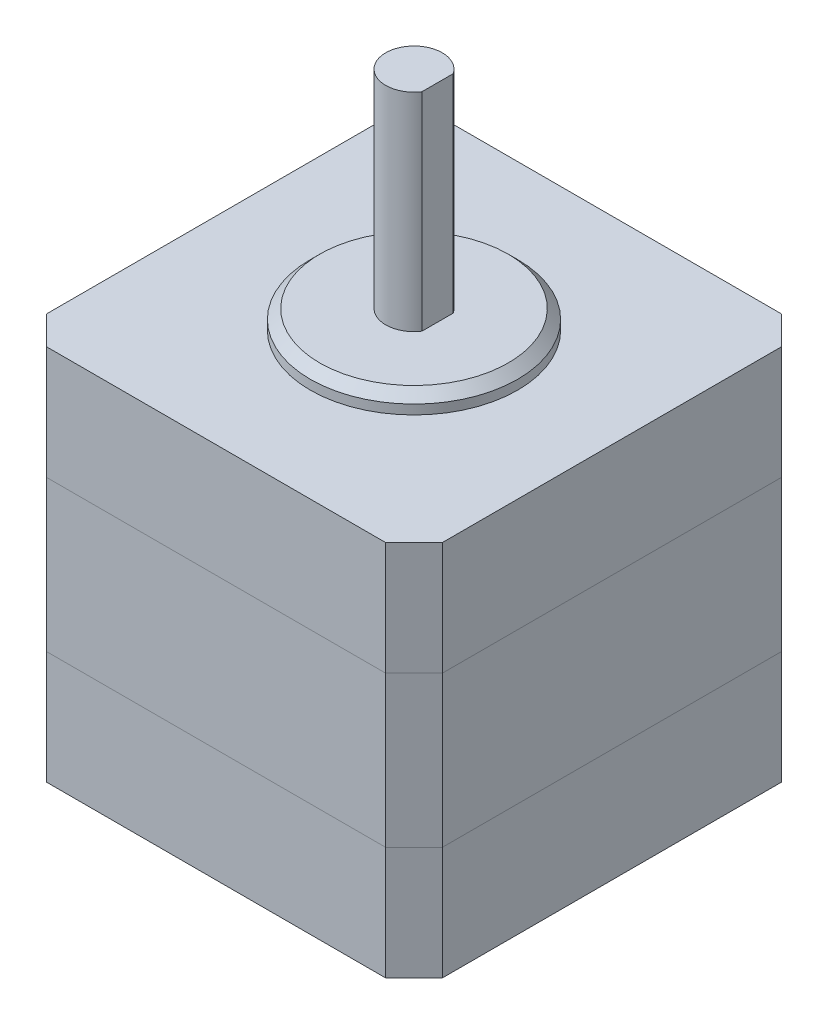
SolidWorks part; units mm, degrees
material "Cast Stainless Steel"
ref_plane "Front Plane" through (0, 0, 0) normal (0, 0, 1) x (1, 0, 0)
ref_plane "Top Plane" through (0, 0, 0) normal (0, 1, 0) x (1, 0, 0)
ref_plane "Right Plane" through (0, 0, 0) normal (1, 0, 0) x (0, 0, -1)
sketch "Sketch1" plane through (0, 0, 0) normal (0, 1, 0) x (1, 0, 0)
  line L1 (-21, -21) -> (21, -21)
  line L2 (-21, -21) -> (-21, 21)
  line L3 (-21, 21) -> (21, 21)
  line L4 (21, -21) -> (21, 21)
  line L5 (-21, -21) -> (21, 21) construction
  line L6 (-21, 21) -> (21, -21) construction
  point P0 (0, 0)
  dimension "D1" = 42
extrude "Boss-Extrude1" add sketch "Sketch1" along normal blind 40
ref_plane "Plane1" through (0, 28, 0) normal (0, 1, 0) x (1, 0, 0)
ref_plane "Plane2" through (0, 12, 0) normal (0, -1, 0) x (-1, 0, 0)
chamfer "Chamfer2" distance 3 angle 45 4 edges at (21, 20, -21) (21, 20, 21) (-21, 20, 21) (-21, 20, -21)
split line "Split Line1"
split line "Split Line2"
sketch "Sketch2" plane through (0, 40, 0) normal (0, 1, 0) x (1, 0, 0)
  circle A0 centre (0, 0) radius 11
  dimension "D1" = 22
extrude "Boss-Extrude2" add sketch "Sketch2" along normal blind 2
sketch "Sketch3" plane through (0, 42, 0) normal (0, 1, 0) x (1, 0, 0)
  line L0 (2.5, 1.6583) -> (2.5, -1.6583)
  arc A0 (2.5, 1.6583) -> (2.5, -1.6583) centre (0, 0) ccw
  dimension "D1" = 6
  dimension "D2" = 2.5
extrude "Boss-Extrude3" add sketch "Sketch3" along normal blind 22
chamfer "Chamfer3" distance 1 angle 45 1 edges at (0, 42, 11)
